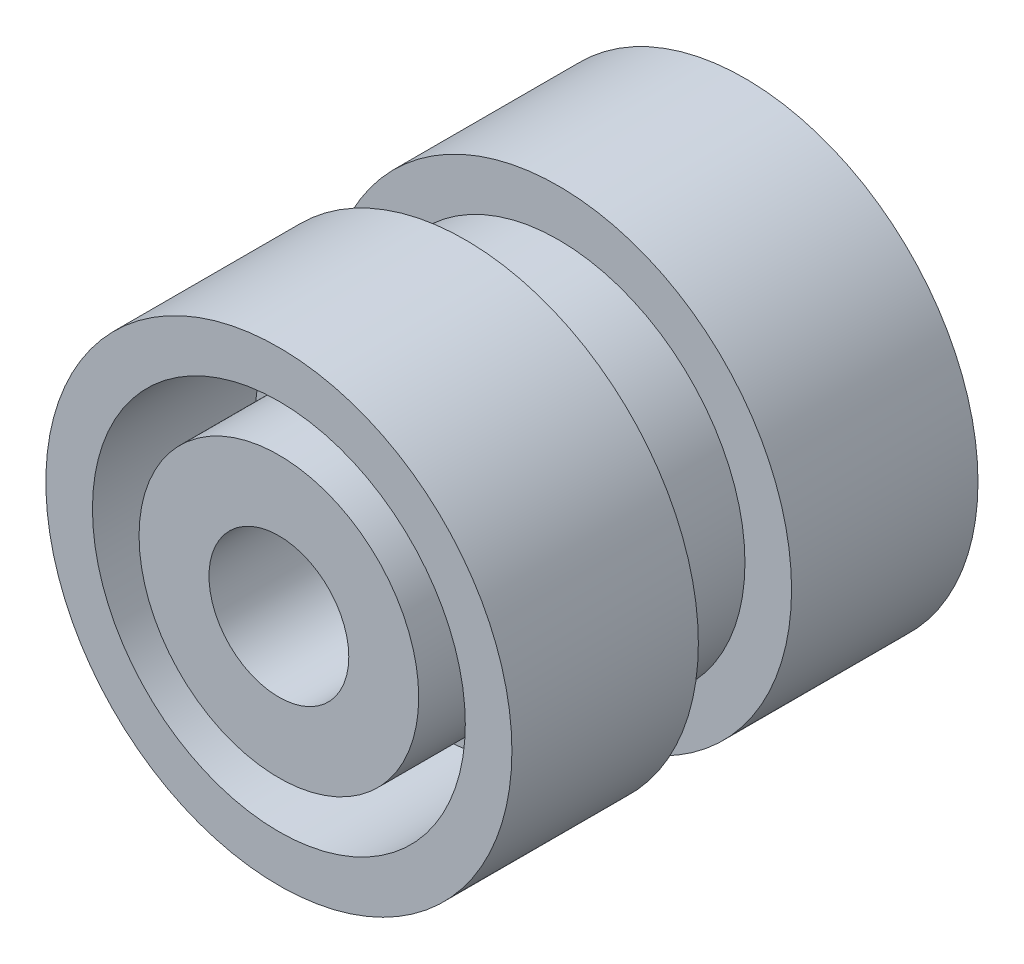
SolidWorks part; units mm, degrees
ref_plane "Front Plane" through (0, 0, 0) normal (0, 0, 1) x (1, 0, 0)
ref_plane "Top Plane" through (0, 0, 0) normal (0, 1, 0) x (1, 0, 0)
ref_plane "Right Plane" through (0, 0, 0) normal (1, 0, 0) x (0, 0, -1)
sketch "Sketch2" plane through (0, 0, 0) normal (1, 0, 0) x (0, 0, -1)
  line L0 (-7.5473, 0) -> (11.2946, 0) construction
  line L1 (0, 0) -> (-5, 0)
  line L2 (-5, 0) -> (-5, 3)
  line L3 (-5, 3) -> (-1.5, 3)
  line L4 (-1.5, 3) -> (-1.5, 4)
  line L5 (-1.5, 4) -> (-5, 4)
  line L6 (-5, 4) -> (-5, 5)
  line L7 (-5, 5) -> (-1, 5)
  line L8 (-1, 5) -> (-1, 4)
  line L9 (-1, 4) -> (1, 4)
  line L10 (0, 4) -> (0, 0) construction
  line L11 (5, 4) -> (5, 5)
  line L12 (1, 5) -> (1, 4)
  line L13 (5, 5) -> (1, 5)
  line L14 (5, 4) -> (1.5, 4)
  line L15 (1.5, 4) -> (1.5, 0)
  line L16 (1.5, 0) -> (0, 0)
  dimension "D1" = 5
  dimension "D2" = 3
  dimension "D3" = 3.5
  dimension "D4" = 1
  dimension "D5" = 3.5
  dimension "D6" = 1
  dimension "D7" = 1
  dimension "D8" = 1
revolve "Revolve1" add sketch "Sketch2" angle 360 about L0
sketch "Sketch3" plane through (0, 0, -1.5) normal (0, 0, -1) x (-1, 0, 0)
  line L0 (0, 0) -> (0, 4) construction
  line L1 (0.5, 1.9365) -> (0.5, 3.9686)
  line L2 (-0.5, 1.9365) -> (-0.5, 3.9686)
  line L3 (-0.5, 0) -> (-0.5, 4) construction
  line L4 (0.5, 0) -> (0.5, 4) construction
  line L5 (1.9365, 0.5) -> (3.9686, 0.5)
  line L6 (1.9365, -0.5) -> (3.9686, -0.5)
  line L7 (0.5, -1.9365) -> (0.5, -3.9686)
  line L8 (-0.5, -1.9365) -> (-0.5, -3.9686)
  line L9 (-1.9365, -0.5) -> (-3.9686, -0.5)
  line L10 (-1.9365, 0.5) -> (-3.9686, 0.5)
  circle A0 centre (0, 0) radius 4 construction
  arc A1 (0.5, 3.9686) -> (-0.5, 3.9686) centre (0, 0) ccw
  arc A2 (-1.9365, -0.5) -> (-0.5, -1.9365) centre (0, 0) ccw
  arc A3 (0.5, -1.9365) -> (1.9365, -0.5) centre (0, 0) ccw
  arc A4 (1.9365, 0.5) -> (0.5, 1.9365) centre (0, 0) ccw
  arc A5 (-0.5, 1.9365) -> (-1.9365, 0.5) centre (0, 0) ccw
  arc A6 (-3.9686, 0.5) -> (-3.9686, -0.5) centre (0, 0) ccw
  arc A7 (-0.5, -3.9686) -> (0.5, -3.9686) centre (0, 0) ccw
  arc A8 (3.9686, -0.5) -> (3.9686, 0.5) centre (0, 0) ccw
  point P28 (0, 0)
  dimension "D1" = 4
  dimension "D2" = 0.5
  dimension "D3" = 0.5
  dimension "D4" = 4
extrude "Boss-Extrude1" add sketch "Sketch3" along normal blind 2
sketch "Sketch4" plane through (0, 0, 5) normal (0, 0, 1) x (1, 0, 0)
  circle A0 centre (0, 0) radius 1.5
  dimension "D1" = 3
extrude "Cut-Extrude1" cut sketch "Sketch4" against normal blind 8 contours A0
scale "Scale1" scale about centroid uniform scaling yes scale factor 2
